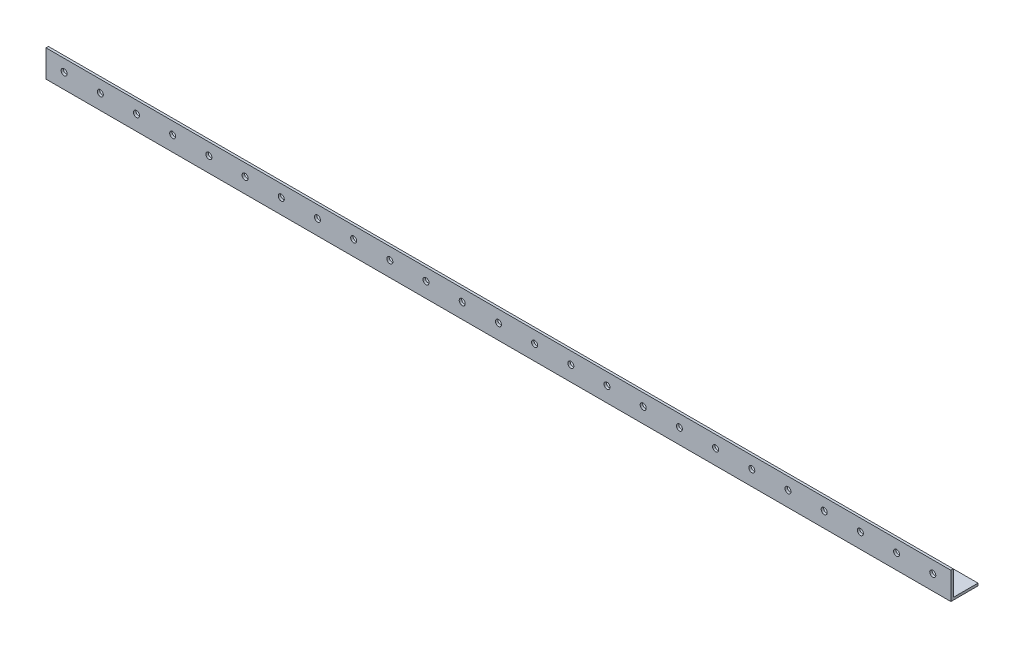
SolidWorks part; units mm, degrees
ref_plane "Спереди" through (0, 0, 0) normal (0, 0, 1) x (1, 0, 0)
ref_plane "Сверху" through (0, 0, 0) normal (0, 1, 0) x (1, 0, 0)
ref_plane "Справа" through (0, 0, 0) normal (1, 0, 0) x (0, 0, -1)
sketch "Эскиз1" plane through (0, 0, 0) normal (1, 0, 0) x (0, 0, -1)
  line L0 (0, 0) -> (0, 45)
  line L1 (0, 0) -> (45, 0)
  dimension "D1" = 45
  dimension "D2" = 45
extrude "Вытянуть-Тонкостенный1" add sketch "Эскиз1" along normal blind 1500 thin
sketch "Эскиз2" plane through (0, 0, 0) normal (0, 0, 1) x (1, 0, 0)
  circle A0 centre (30, 25) radius 5
  circle A1 centre (90, 25) radius 5
  circle A2 centre (150, 25) radius 5
  circle A3 centre (210, 25) radius 5
  circle A8 centre (270, 25) radius 5
  circle A9 centre (330, 25) radius 5
  circle A10 centre (390, 25) radius 5
  circle A11 centre (450, 25) radius 5
  circle A12 centre (510, 25) radius 5
  circle A13 centre (570, 25) radius 5
  circle A14 centre (630, 25) radius 5
  circle A15 centre (690, 25) radius 5
  circle A16 centre (750, 25) radius 5
  circle A17 centre (810, 25) radius 5
  circle A18 centre (870, 25) radius 5
  circle A19 centre (930, 25) radius 5
  circle A20 centre (990, 25) radius 5
  circle A21 centre (1050, 25) radius 5
  circle A22 centre (1110, 25) radius 5
  circle A23 centre (1170, 25) radius 5
  circle A24 centre (1230, 25) radius 5
  circle A25 centre (1290, 25) radius 5
  circle A26 centre (1350, 25) radius 5
  circle A27 centre (1410, 25) radius 5
  circle A28 centre (1470, 25) radius 5
  dimension "D1" = 25
extrude "Вырез-Вытянуть1" cut sketch "Эскиз2" against normal through all
sketch "Эскиз3" plane through (0, 0, 0) normal (0, -1, 0) x (1, 0, 0)
  circle A0 centre (30, -25) radius 5
  circle A1 centre (90, -25) radius 5
  circle A2 centre (150, -25) radius 5
  circle A3 centre (210, -25) radius 5
  circle A4 centre (270, -25) radius 5
  circle A5 centre (330, -25) radius 5
  circle A6 centre (390, -25) radius 5
  circle A7 centre (450, -25) radius 5
  circle A8 centre (510, -25) radius 5
  circle A9 centre (570, -25) radius 5
  circle A10 centre (630, -25) radius 5
  circle A11 centre (690, -25) radius 5
  circle A12 centre (750, -25) radius 5
  circle A13 centre (810, -25) radius 5
  circle A14 centre (870, -25) radius 5
  circle A15 centre (930, -25) radius 5
  circle A16 centre (990, -25) radius 5
  circle A17 centre (1050, -25) radius 5
  circle A18 centre (1110, -25) radius 5
  circle A19 centre (1170, -25) radius 5
  circle A20 centre (1230, -25) radius 5
  circle A21 centre (1290, -25) radius 5
  circle A22 centre (1350, -25) radius 5
  circle A23 centre (1410, -25) radius 5
  circle A24 centre (1470, -25) radius 5
  dimension "D1" = 25
extrude "Вырез-Вытянуть2" cut sketch "Эскиз3" against normal through all
